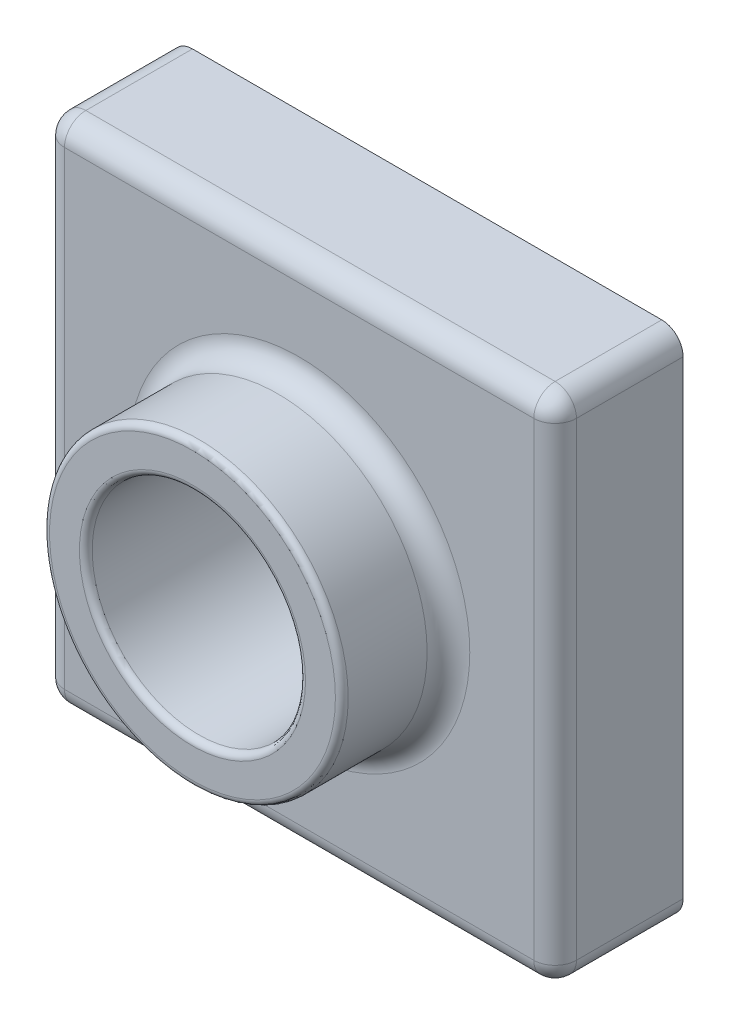
SolidWorks part; units mm, degrees
ref_plane "Front Plane" through (0, 0, 0) normal (0, 0, 1) x (1, 0, 0)
ref_plane "Top Plane" through (0, 0, 0) normal (0, 1, 0) x (1, 0, 0)
ref_plane "Right Plane" through (0, 0, 0) normal (1, 0, 0) x (0, 0, -1)
sketch "Sketch1" plane through (0, 0, 0) normal (0, 0, 1) x (1, 0, 0)
  line L1 (0, 120) -> (120, 120)
  line L2 (0, 120) -> (0, 0)
  line L3 (0, 0) -> (120, 0)
  line L4 (120, 120) -> (120, 0)
  point P4 (0, 0)
  point P7 (0, 0)
  dimension "D1" = 120
  dimension "D2" = 120
extrude "Boss-Extrude1" add sketch "Sketch1" along normal blind 30
sketch "Sketch2" plane through (0, 0, 30) normal (0, 0, 1) x (1, 0, 0)
sketch "Sketch3" plane through (0, 0, 30) normal (0, 0, 1) x (1, 0, 0)
  line L1 (120, 120) -> (0, 120) construction
  line L2 (0, 120) -> (0, 0) construction
  circle A0 centre (60, 60) radius 35
  point P6 (74.2722, 58.0908)
  dimension "D1" = 70
  dimension "D2" = 60
  dimension "D3" = 60
extrude "Boss-Extrude2" add sketch "Sketch3" along normal blind 25
sketch "Sketch4" plane through (0, 0, 55) normal (0, 0, 1) x (1, 0, 0)
  circle A0 centre (60, 60) radius 25
  dimension "D1" = 50
extrude "Cut-Extrude1" cut sketch "Sketch4" against normal through all
fillet "Fillet1" radius 5 9 edges at (60, 120, 30) (120, 60, 30) (60, 0, 30) (0, 60, 30) (95, 60, 30) (120, 120, 15) (0, 120, 15) (0, 0, 15) (120, 0, 15)
fillet "Fillet2" radius 1.5 2 edges at (95, 60, 55) (85, 60, 55)
shell "Shell1" thickness 2
